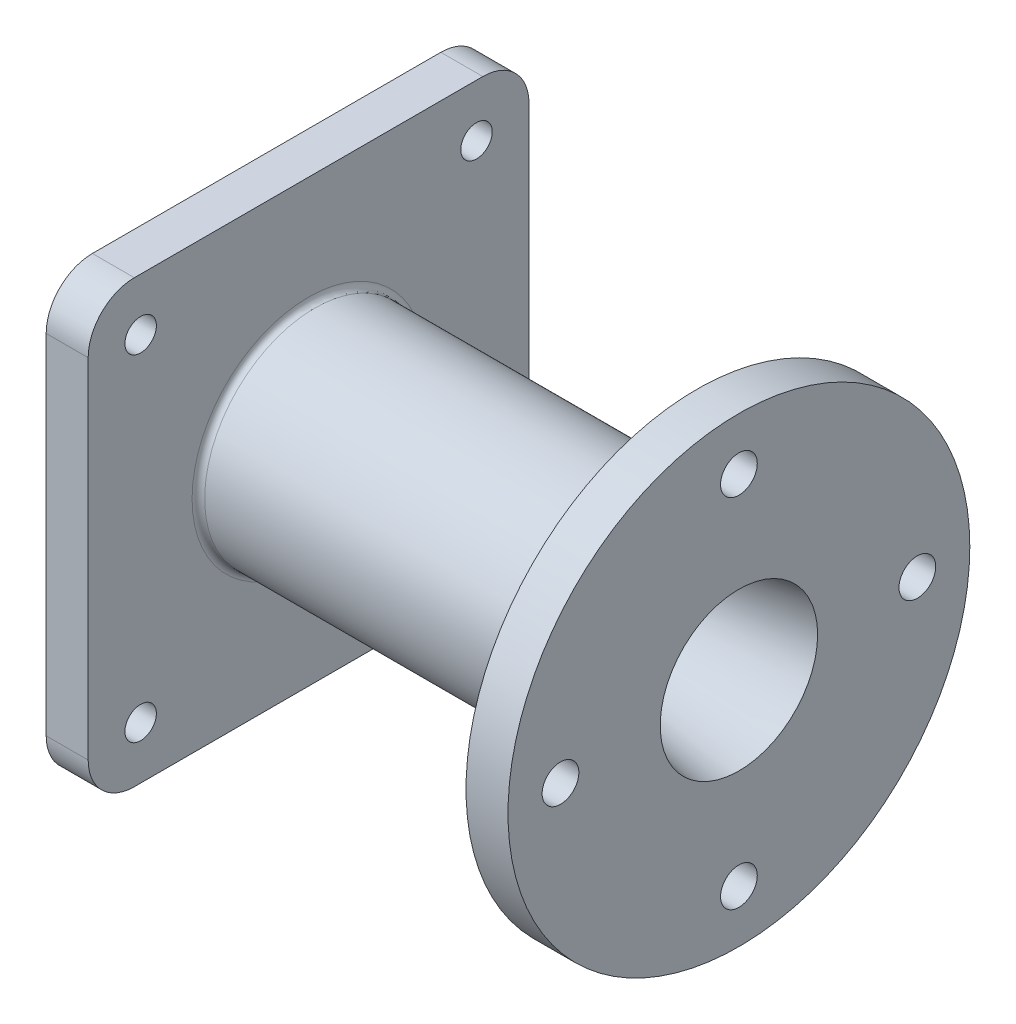
SolidWorks part; units mm, degrees
material "Сталь"
ref_plane "Спереди" through (0, 0, 0) normal (0, 0, 1) x (1, 0, 0)
ref_plane "Сверху" through (0, 0, 0) normal (0, 1, 0) x (1, 0, 0)
ref_plane "Справа" through (0, 0, 0) normal (1, 0, 0) x (0, 0, -1)
sketch "Эскиз1" plane through (0, 0, 0) normal (0, 0, 1) x (1, 0, 0)
  line L0 (0, 0) -> (-243.1706, 0) construction
  line L1 (0, 37.5) -> (0, 110)
  line L2 (0, 110) -> (-20, 110)
  line L3 (-20, 110) -> (-20, 60)
  line L4 (-20, 60) -> (-55, 52.5)
  line L5 (-55, 52.5) -> (-205, 52.5)
  line L6 (-205, 52.5) -> (-205, 105)
  line L7 (-205, 105) -> (-225, 105)
  line L8 (-225, 105) -> (-225, 62.5)
  line L9 (-225, 62.5) -> (-210, 62.5)
  line L10 (-210, 62.5) -> (-210, 28.7125)
  line L11 (-210, 28.7125) -> (-160, 28.7125)
  line L12 (0, 37.5) -> (-77.5, 25)
  line L13 (-77.5, 25) -> (-77.5, 28.7125)
  line L14 (-77.5, 28.7125) -> (-95, 28.7125)
  line L15 (-95, 28.7125) -> (-95, 40)
  line L16 (-95, 40) -> (-160, 40)
  line L17 (-160, 40) -> (-160, 28.7125)
  dimension "D1" = 220
  dimension "D2" = 20
  dimension "D3" = 75
  dimension "D4" = 105
  dimension "D5" = 120
  dimension "D6" = 35
  dimension "D7" = 150
  dimension "D8" = 210
  dimension "D9" = 210
  dimension "D10" = 125
  dimension "D11" = 57.425
  dimension "D12" = 50
  dimension "D13" = 77.5
  dimension "D14" = 80
  dimension "D15" = 65
  dimension "D16" = 95
revolve "Повернуть1" add sketch "Эскиз1" angle 360 about L0
cosmetic thread "Условное изображение резьбы1" parameters "D2"=64
sketch "Эскиз2" plane through (0, 0, 0) normal (1, 0, 0) x (0, 0, -1)
  circle A0 centre (0, 85) radius 8.75
  dimension "D2" = 17.5
  dimension "D1" = 85
extrude "Вырез-Вытянуть1" cut sketch "Эскиз2" against normal up to next
pattern_circular "Круговой массив1" count 4 over 360 about axis through (0, 0, 0) along (1, 0, 0) of "Вырез-Вытянуть1"
sketch "Эскиз3" plane through (-225, 0, 0) normal (-1, 0, 0) x (0, 0, 1)
  line L1 (-105, -105) -> (105, -105)
  line L2 (-105, -105) -> (-105, 105)
  line L3 (-105, 105) -> (105, 105)
  line L4 (105, -105) -> (105, 105)
  line L5 (-105, -105) -> (105, 105) construction
  line L6 (-105, 105) -> (105, -105) construction
  circle A0 centre (0, 0) radius 105 construction
  circle A2 centre (0, 0) radius 28.7125 construction
  circle A3 centre (0, 0) radius 28.7125
  point P0 (0, 0)
extrude "Бобышка-Вытянуть1" add sketch "Эскиз3" against normal up to surface (20 mm away) up to face at (-205, 0, -105)
sketch "Эскиз4" plane through (-225, 0, 0) normal (-1, 0, 0) x (0, 0, 1)
  line L0 (0, 0) -> (105, 105) construction
  circle A0 centre (80, 80) radius 7.5
  dimension "D1" = 80
  dimension "D2" = 15
extrude "Вырез-Вытянуть2" cut sketch "Эскиз4" against normal up to surface (20 mm away) up to face at (-205, 0, 0)
fillet "Скругление1" radius 22 4 edges at (-215, 105, 105) (-215, -105, 105) (-215, -105, -105) (-215, 105, -105)
pattern_circular "Круговой массив5" count 4 over 360 about axis through (0, 0, 0) along (1, 0, 0) of "Вырез-Вытянуть2"
fillet "Скругление2" radius 3 2 edges at (-160, 0, -40) (-95, 0, -40)
sketch "Эскиз5" plane through (-77.5, 0, 0) normal (-1, 0, 0) x (0, 0, 1)
  circle A0 centre (0, 0) radius 28.7125 construction
  circle A1 centre (0, 0) radius 28.7125
  circle A2 centre (0, 0) radius 27.5
  dimension "D1" = 55
extrude "Бобышка-Вытянуть2" add sketch "Эскиз5" along normal up to surface (17.5 mm away) up to face at (-95, 0, 37)
fillet "Скругление3" radius 3 2 edges at (-20, 0, -60) (-205, 0, -52.5)
